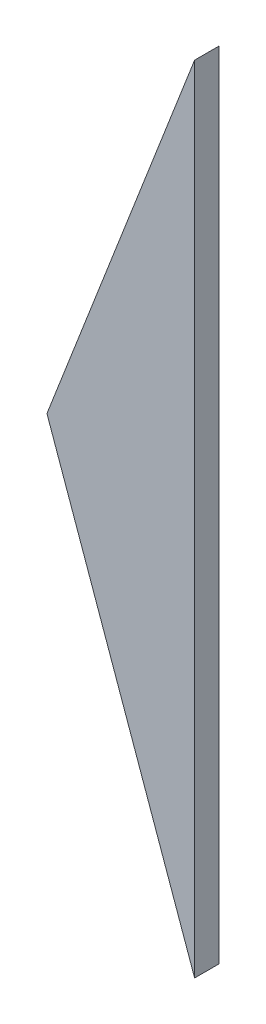
SolidWorks part; units mm, degrees
ref_plane "Plan de face" through (0, 0, 0) normal (0, 0, 1) x (1, 0, 0)
ref_plane "Plan de dessus" through (0, 0, 0) normal (0, 1, 0) x (1, 0, 0)
ref_plane "Plan de droite" through (0, 0, 0) normal (1, 0, 0) x (0, 0, -1)
sketch "Esquisse1" plane through (0, 0, 0) normal (0, 0, 1) x (1, 0, 0)
  line L0 (-25.7431, -66.2226) -> (-7.627, -19.62)
  line L1 (-7.627, -19.62) -> (-7.627, -117.1347)
  line L2 (-7.627, -117.1347) -> (-25.7431, -66.2226)
  line L3 (0, 0) -> (-26.1476, -67.2634) construction
  line L4 (2.5315, -145.6832) -> (-26.1174, -65.1707) construction
  point P7 (-9.4386, -112.0435)
  dimension "D1" = 50
extrude "Boss.-Extru.1" add sketch "Esquisse1" against normal blind 3
